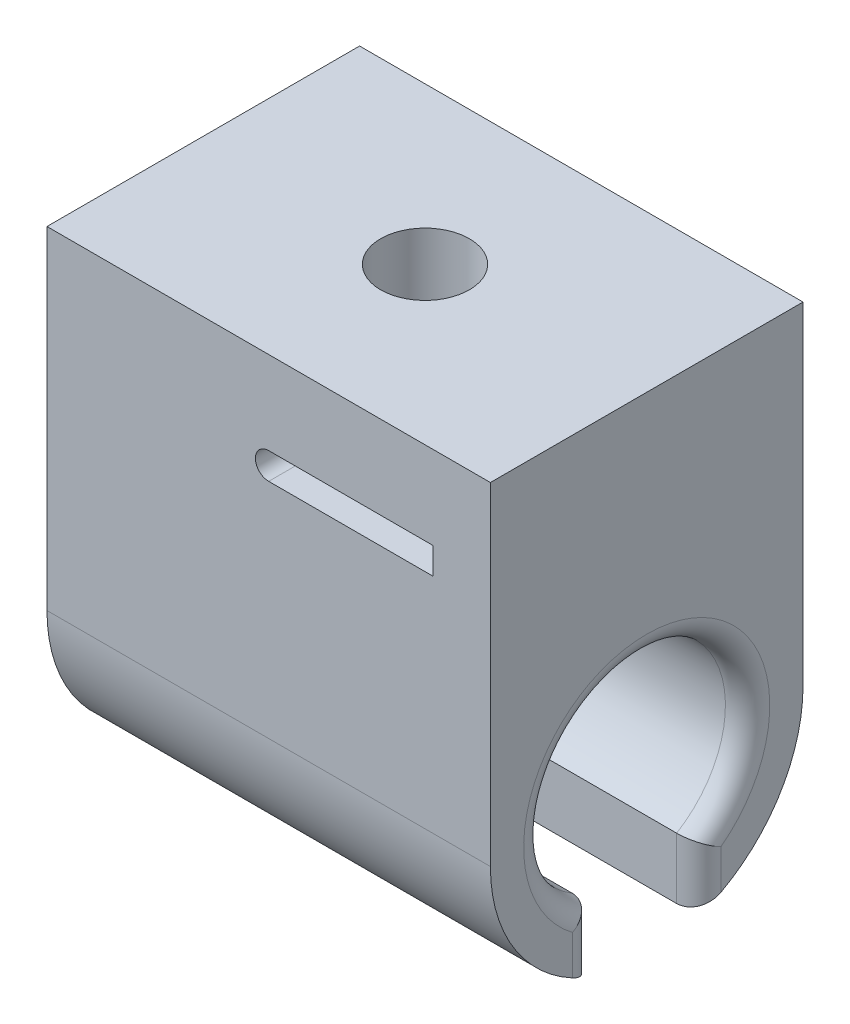
SolidWorks part; units mm, degrees
ref_plane "Front Plane" through (0, 0, 0) normal (0, 0, 1) x (1, 0, 0)
ref_plane "Top Plane" through (0, 0, 0) normal (0, 1, 0) x (1, 0, 0)
ref_plane "Right Plane" through (0, 0, 0) normal (1, 0, 0) x (0, 0, -1)
sketch "Sketch1" plane through (0, 0, 0) normal (1, 0, 0) x (0, 0, -1)
  line L2 (-8.9535, 0) -> (-8.9535, 19.05)
  line L3 (-8.9535, 19.05) -> (8.9535, 19.05)
  line L4 (8.9535, 0) -> (8.9535, 19.05)
  circle A0 centre (0, 0) radius 8.9535
  circle A1 centre (0, 0) radius 5.7785
  dimension "D2" = 11.557
  dimension "D3" = 19.05
  dimension "D1" = 3.175
extrude "Boss-Extrude1" add sketch "Sketch1" along normal blind 25.4
sketch "Sketch2" plane through (0, 19.05, 0) normal (0, 1, 0) x (1, 0, 0)
  line L0 (25.4, 8.9535) -> (0, 8.9535) construction
  line L1 (0, -8.9535) -> (0, 8.9535) construction
  circle A0 centre (12.7, 0) radius 2.54
  point P5 (12.7, 8.9535)
  point P11 (0, 0)
  dimension "D1" = 5.08
extrude "Cut-Extrude1" cut sketch "Sketch2" against normal up to surface (27.6357 mm away)
sketch "Sketch3" plane through (0, 0, 0) normal (-1, 0, 0) x (0, 0, 1)
  line L1 (-2.9845, -8.9535) -> (2.9845, -8.9535)
  line L2 (-2.9845, -8.9535) -> (-2.9845, -4.9481)
  line L3 (-2.9845, -4.9481) -> (2.9845, -4.9481)
  line L4 (2.9845, -8.9535) -> (2.9845, -4.9481)
  circle A0 centre (0, 0) radius 5.7785 construction
  arc A1 (-8.9535, 0) -> (8.9535, 0) centre (0, 0) ccw construction
  dimension "D1" = 2.9845
  dimension "D2" = 2.9845
extrude "Cut-Extrude2" cut sketch "Sketch3" against normal through all
fillet "Fillet1" radius 1.27 6 edges at (0, -6.6948, 2.9845) (0, -6.6948, -2.9845) (0, 5.7785, 0) (25.4, -6.6948, -2.9845) (25.4, -6.6948, 2.9845) (25.4, 5.7785, 0)
fillet "Fillet2" [suppressed] radius 1.27
sketch "Sketch5" [suppressed] plane through (0, 0, -8.9535) normal (0, 0, -1) x (-1, 0, 0)
  line L0 (-25.4, 7.0485) -> (-25.4, -5.6197) construction
  line L1 (-25.4, 7.0485) -> (-25.4, -5.6197)
  line L2 (-24.13, 25.4) -> (-1.27, 25.4) construction
  dimension "D1" = 18.3515
sketch "Sketch6" plane through (16.4465, 0, -8.9535) normal (0, 0, 1) x (1, 0, 0)
  line L1 (-4.5085, 14.2822) -> (5.6515, 14.2822)
  line L2 (-4.5085, 14.2822) -> (-4.5085, 12.7582)
  line L3 (-4.5085, 12.7582) -> (5.6515, 12.7582)
  line L4 (5.6515, 14.2822) -> (5.6515, 12.7582)
  circle A0 centre (-3.7465, 13.5202) radius 0.762
  line M22 (8.9535, 19.05) -> (8.9535, 0)
  dimension "D1" = 1.524
  dimension "D5" = 10.16
extrude "Cut-Extrude4" cut sketch "Sketch6" along normal through all contours L3 L2 L1 A0 M22 | A0
